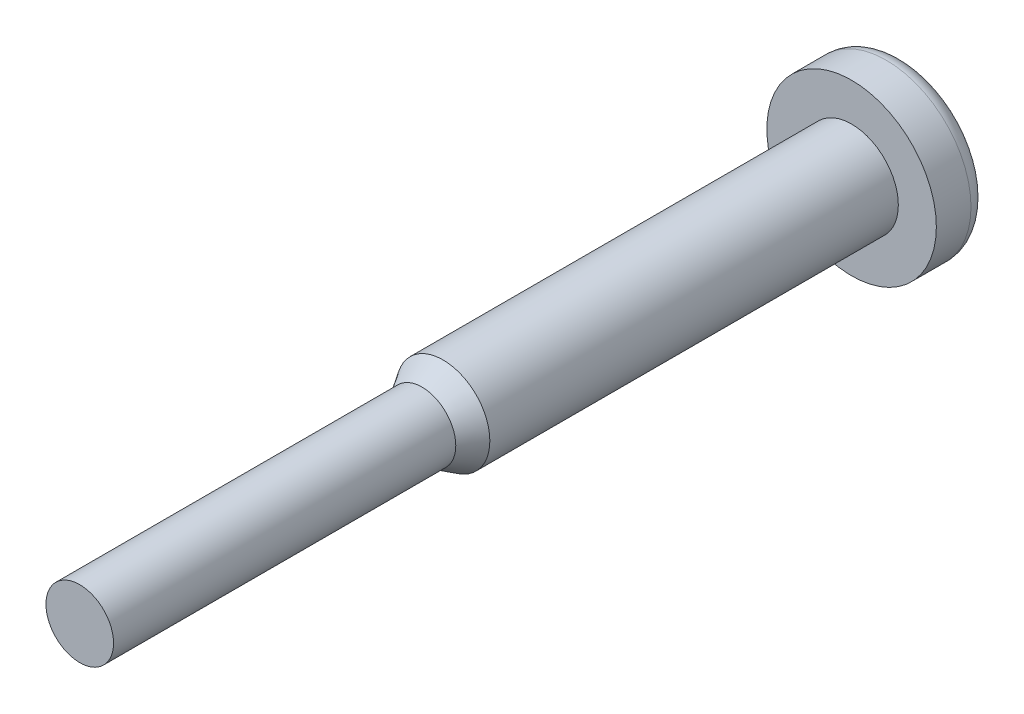
SolidWorks part; units mm, degrees
material "1023 Tôle d'acier au carbone (SS)"
ref_plane "Plan de face" through (0, 0, 0) normal (0, 0, 1) x (1, 0, 0)
ref_plane "Plan de dessus" through (0, 0, 0) normal (0, 1, 0) x (1, 0, 0)
ref_plane "Plan de droite" through (0, 0, 0) normal (1, 0, 0) x (0, 0, -1)
sketch "Esquisse1" plane through (0, 0, 0) normal (1, 0, 0) x (0, 0, -1)
  line L0 (0, 0) -> (97.44, 0) construction
  line L1 (97.44, 0) -> (97.44, 8.03)
  line L2 (95.44, 10.03) -> (91.34, 10.03)
  line L3 (91.34, 10.03) -> (91.34, 5.53)
  line L4 (91.34, 5.53) -> (43, 5.53)
  line L5 (43, 5.53) -> (40.5, 4)
  line L6 (40.5, 4) -> (0, 4)
  line L7 (0, 4) -> (0, 0)
  line L8 (0, 0) -> (97.44, 0)
  arc A0 (97.44, 8.03) -> (95.44, 10.03) centre (95.44, 8.03) ccw
  point P11 (97.44, 10.03)
  dimension "D8" = 2
  dimension "D1" = 4
  dimension "D2" = 40.5
  dimension "D3" = 5.53
  dimension "D4" = 2.5
  dimension "D5" = 6.1
  dimension "D6" = 4.5
  dimension "D7" = 97.44
revolve "Révolution1" add sketch "Esquisse1" angle 360 about L0
